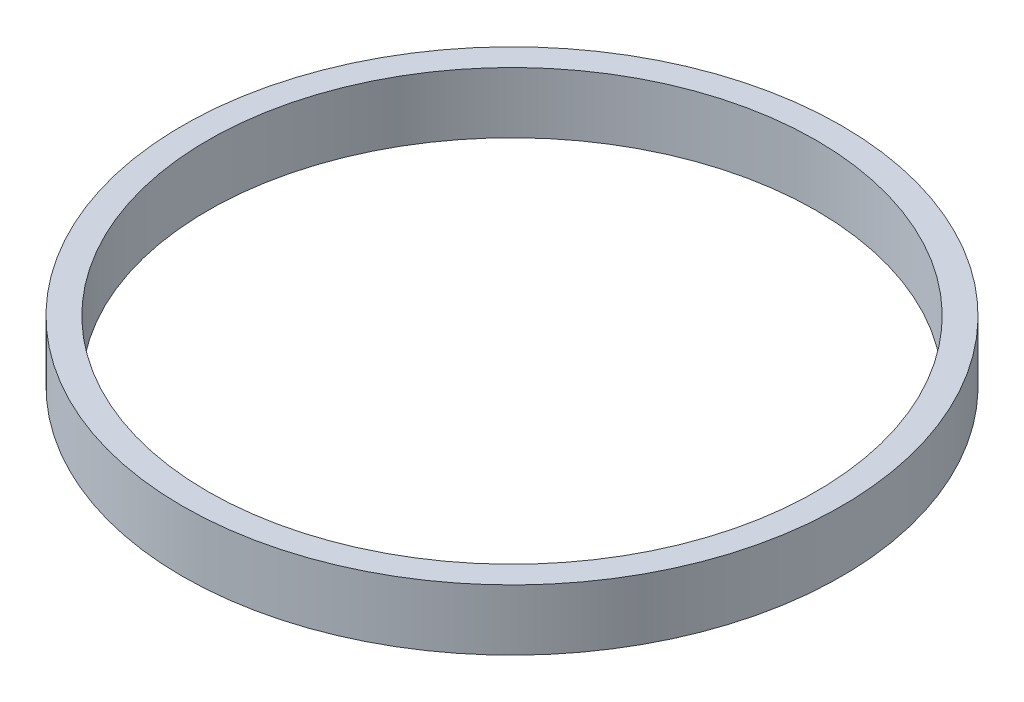
SolidWorks part; units mm, degrees
material "PP Copolymer"
ref_plane "Front Plane" through (0, 0, 0) normal (0, 0, 1) x (1, 0, 0)
ref_plane "Top Plane" through (0, 0, 0) normal (0, 1, 0) x (1, 0, 0)
ref_plane "Right Plane" through (0, 0, 0) normal (1, 0, 0) x (0, 0, -1)
sketch "Sketch1" plane through (0, 0, 0) normal (0, 1, 0) x (1, 0, 0)
  circle A0 centre (0, 0) radius 32.5
  circle A1 centre (0, 0) radius 30
  dimension "D1" = 65
  dimension "D2" = 2.5
extrude "Boss-Extrude1" add sketch "Sketch1" along normal blind 6
